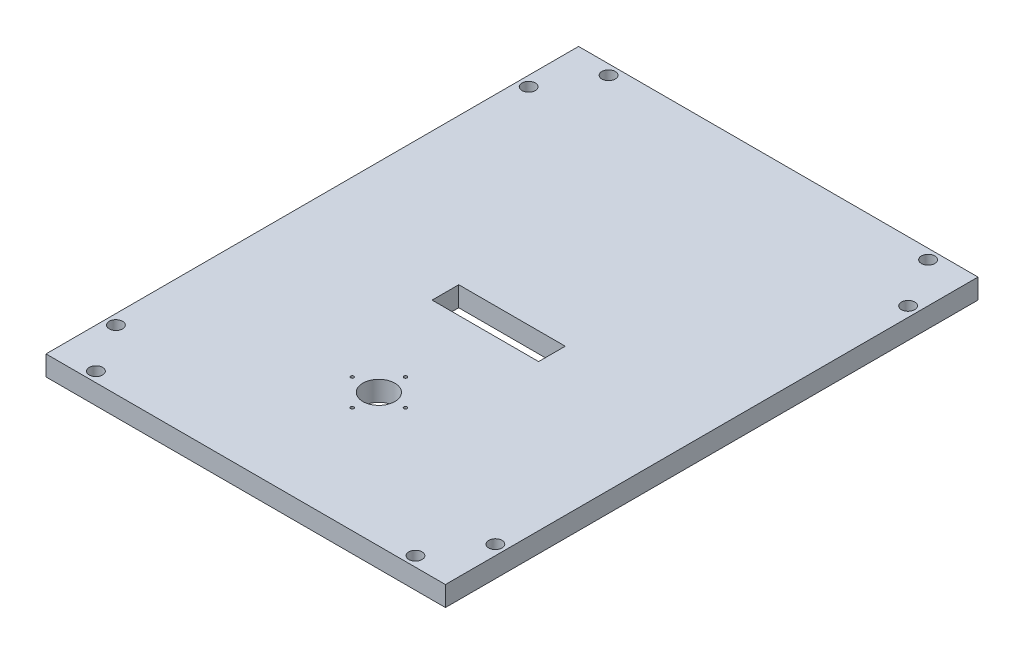
SolidWorks part; units mm, degrees
ref_plane "Front Plane" through (0, 0, 0) normal (0, 0, 1) x (1, 0, 0)
ref_plane "Top Plane" through (0, 0, 0) normal (0, 1, 0) x (1, 0, 0)
ref_plane "Right Plane" through (0, 0, 0) normal (1, 0, 0) x (0, 0, -1)
sketch "Croquis1" plane through (0, 0, 0) normal (0, 1, 0) x (1, 0, 0)
  line L0 (0, 100) -> (150, 100)
  line L1 (0, 0) -> (150, 0)
  line L2 (0, 0) -> (0, 200)
  line L3 (0, 200) -> (150, 200)
  line L4 (150, 0) -> (150, 200)
  line L7 (75, 90) -> (55, 90)
  line L8 (55, 90) -> (55, 100)
  line L9 (55, 100) -> (95, 100)
  line L10 (95, 100) -> (95, 90)
  line L11 (95, 90) -> (75, 90)
  circle A0 centre (75, 50) radius 6
  circle A5 centre (85, 50) radius 0.6
  circle A6 centre (75, 40) radius 0.6
  circle A7 centre (65, 50) radius 0.6
  circle A8 centre (75, 60) radius 0.6
  point P23 (75, 50)
  point P28 (75, 50)
  dimension "D1" = 4
extrude "Saliente-Extruir2" add sketch "Croquis1" along normal blind 7.5 contours L0 L4 L3 L2 | L10 L11 L7 L8 L0 L2 L1 L4 A8 A7 A6 A5 A0
sketch3d "Croquis3D1"
  point P0 (26.104, 0, -104.5809)
sketch "Croquis4" plane through (0, 0, 0) normal (0, -1, 0) x (1, 0, 0)
  circle A0 centre (135, -3.75) radius 2.5
  circle A1 centre (146.25, -22.5) radius 2.5
  circle A2 centre (3.75, -22.5) radius 2.5
  circle A3 centre (15, -3.75) radius 2.5
  circle A4 centre (146.25, -177.5) radius 2.5
  circle A5 centre (135, -196.25) radius 2.5
  circle A6 centre (3.75, -177.5) radius 2.5
  circle A7 centre (15, -196.25) radius 2.5
extrude "Cortar-Extruir1" cut sketch "Croquis4" against normal blind 7.5
